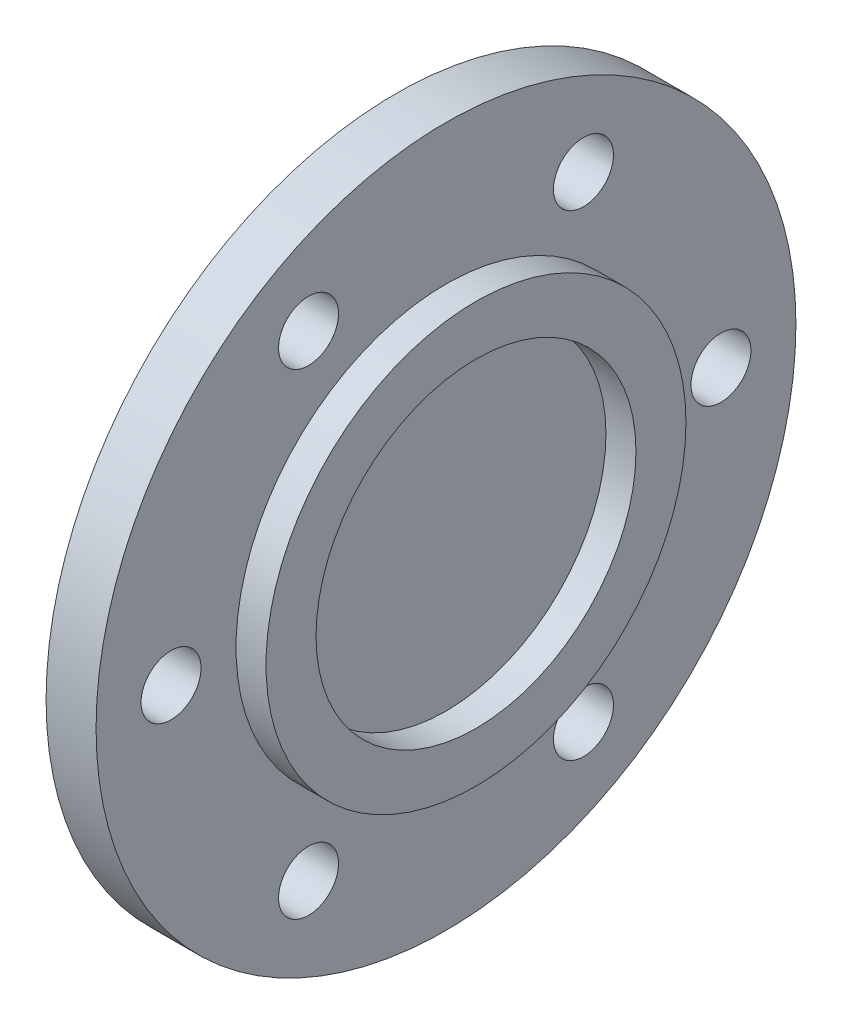
SolidWorks part; units mm, degrees
ref_plane "Front Plane" through (0, 0, 0) normal (0, 0, 1) x (1, 0, 0)
ref_plane "Top Plane" through (0, 0, 0) normal (0, 1, 0) x (1, 0, 0)
ref_plane "Right Plane" through (0, 0, 0) normal (1, 0, 0) x (0, 0, -1)
sketch "Sketch1" plane through (0, 0, 0) normal (0, 0, 1) x (1, 0, 0)
  line L0 (0, 35) -> (5, 35)
  line L1 (5, 35) -> (5, 21)
  line L2 (5, 21) -> (8, 21)
  line L3 (8, 21) -> (8, 16)
  line L4 (8, 16) -> (5, 16)
  line L5 (5, 16) -> (5, 0)
  line L6 (5, 0) -> (0, 0)
  line L7 (0, 0) -> (0, 35)
  dimension "D1" = 35
  dimension "D2" = 5
  dimension "D3" = 3
  dimension "D4" = 3
  dimension "D5" = 5
  dimension "D6" = 21
revolve "Revolve1" add sketch "Sketch1" angle 360 about L6
sketch "Sketch2" plane through (5, 0, 0) normal (1, 0, 0) x (0, 0, -1)
  circle A0 centre (0, 0) radius 27.5 construction
  circle A1 centre (27.5, 0) radius 3
  dimension "D1" = 55
  dimension "D2" = 6
extrude "Cut-Extrude1" cut sketch "Sketch2" against normal blind 10
pattern_circular "CirPattern1" count 6 over 360 about axis through (0, 0, 0) along (1, 0, 0) of "Cut-Extrude1"
